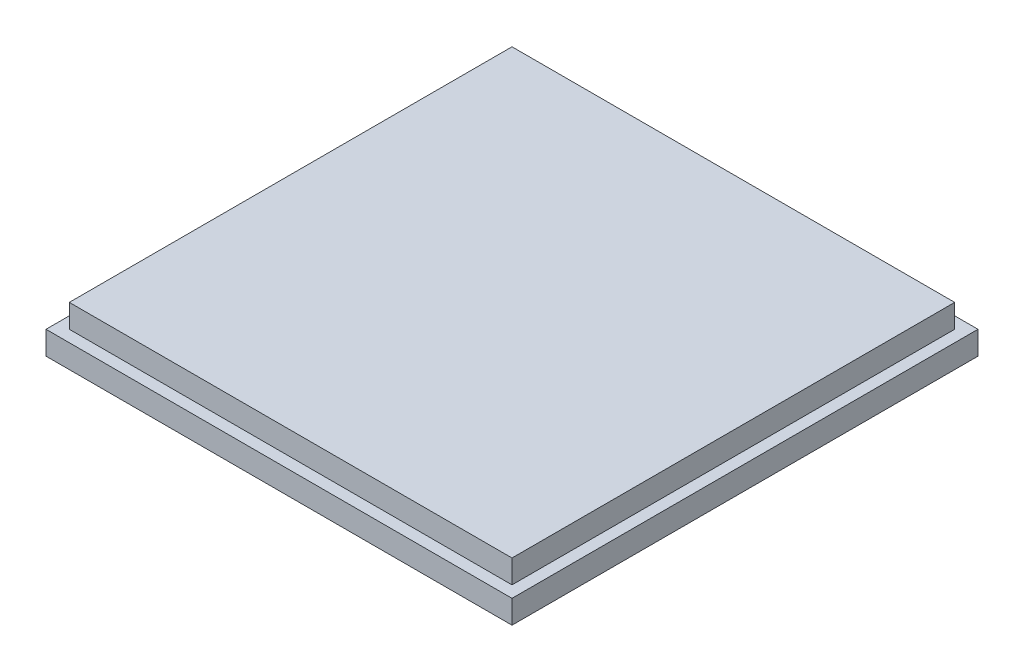
SolidWorks part; units mm, degrees
ref_plane "Front Plane" through (0, 0, 0) normal (0, 0, 1) x (1, 0, 0)
ref_plane "Top Plane" through (0, 0, 0) normal (0, 1, 0) x (1, 0, 0)
ref_plane "Right Plane" through (0, 0, 0) normal (1, 0, 0) x (0, 0, -1)
sketch "Sketch1" plane through (0, 0, 0) normal (0, 1, 0) x (1, 0, 0)
  line L1 (0, 0) -> (50.8, 0)
  line L2 (0, 0) -> (0, 50.8)
  line L3 (0, 50.8) -> (50.8, 50.8)
  line L4 (50.8, 0) -> (50.8, 50.8)
  dimension "D1" = 50.8
extrude "Boss-Extrude1" add sketch "Sketch1" along normal blind 2.54
sketch "Sketch2" plane through (0, 2.54, 0) normal (0, 1, 0) x (1, 0, 0)
  line L0 (0, 50.8) -> (0, 0) construction
  line L1 (1.27, 1.27) -> (49.53, 1.27)
  line L2 (1.27, 1.27) -> (1.27, 49.53)
  line L3 (1.27, 49.53) -> (49.53, 49.53)
  line L4 (49.53, 1.27) -> (49.53, 49.53)
  line L5 (0, 0) -> (50.8, 0) construction
  dimension "D1" = 48.26
  dimension "D2" = 1.27
  dimension "D3" = 1.27
extrude "Boss-Extrude2" add sketch "Sketch2" along normal blind 2.54
